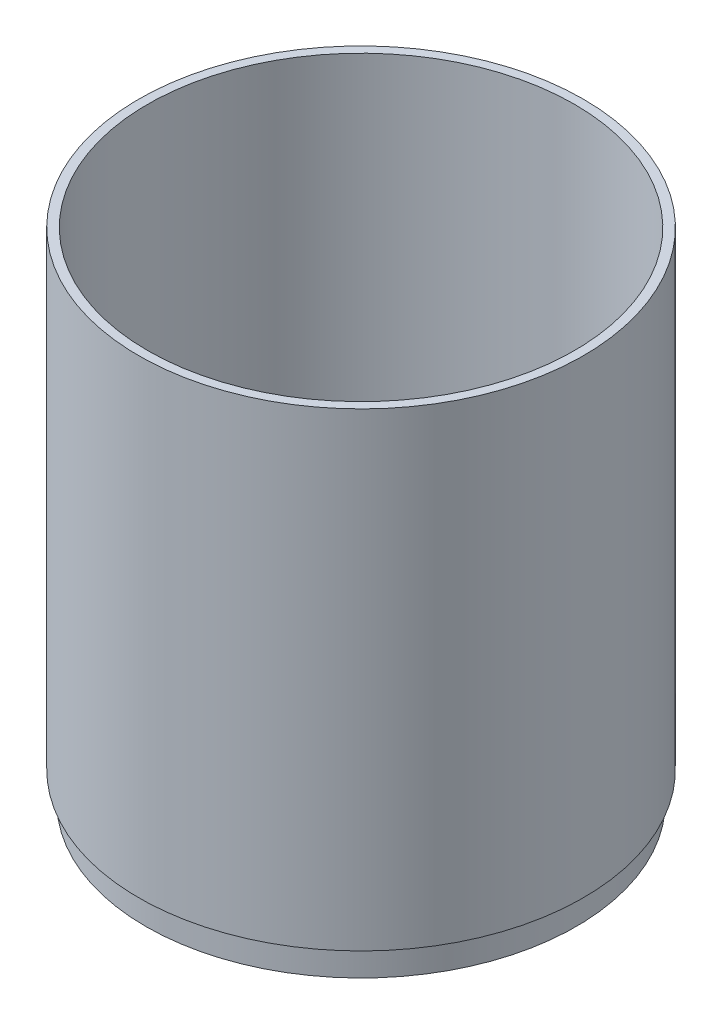
SolidWorks part; units mm, degrees
ref_plane "Front Plane" through (0, 0, 0) normal (0, 0, 1) x (1, 0, 0)
ref_plane "Top Plane" through (0, 0, 0) normal (0, 1, 0) x (1, 0, 0)
ref_plane "Right Plane" through (0, 0, 0) normal (1, 0, 0) x (0, 0, -1)
sketch "Sketch1" plane through (0, 0, 0) normal (0, 0, 1) x (1, 0, 0)
  line L0 (0, 0) -> (0, 40.3893) construction
  line L1 (60.5, 0) -> (15, 0)
  line L2 (60.5, 0) -> (60.5, 8)
  line L3 (60.5, 8) -> (62.5, 8)
  line L4 (62.5, 8) -> (62.5, 140)
  line L5 (62.5, 140) -> (60, 140)
  line L6 (58.5, 10) -> (58.5, 4)
  line L7 (58.5, 4) -> (15, 4)
  line L8 (15, 4) -> (15, 0)
  line L9 (58.5, 10) -> (60, 10)
  line L10 (60, 10) -> (60, 140)
  dimension "D1" = 15
  dimension "D2" = 2
  dimension "D3" = 4
  dimension "D4" = 2
  dimension "D5" = 2
  dimension "D6" = 2.5
  dimension "D7" = 62.5
  dimension "D8" = 140
  dimension "D9" = 8
revolve "Revolve1" add sketch "Sketch1" angle 360 about L0
sketch "Sketch2" plane through (0, 4, 0) normal (0, 1, 0) x (1, 0, 0)
  line L0 (0, 0) -> (0, 58.5) construction
  line L1 (0, 0) -> (-22.387, 54.047)
  line L2 (0, 0) -> (22.387, 54.047)
  line L3 (0, 4) -> (-58.5, 4)
  line L4 (-4, 0) -> (4, 0)
  line L5 (-4, 0) -> (-4, -58.5)
  line L6 (-4, -58.5) -> (4, -58.5)
  line L7 (4, 0) -> (4, -58.5)
  line L8 (0, 4) -> (0, -4)
  line L9 (0, -4) -> (-58.5, -4)
  line L10 (-58.5, 4) -> (-58.5, -4)
  line L11 (4, 0) -> (4, 58.5)
  line L12 (4, 0) -> (-4, 0)
  line L13 (-4, 0) -> (-4, 58.5)
  line L14 (4, 58.5) -> (-4, 58.5)
  line L15 (0, -4) -> (58.5, -4)
  line L16 (0, -4) -> (0, 4)
  line L17 (0, 4) -> (58.5, 4)
  line L18 (58.5, -4) -> (58.5, 4)
  line L19 (0, 0) -> (-4, 0) construction
  line L20 (0, 0) -> (0, 4) construction
  circle A0 centre (0, 0) radius 20
  circle A1 centre (0, 0) radius 58.5
  circle A2 centre (0, 0) radius 58.5
  circle M8 centre (0, 0) radius 58.5
  dimension "D2" = 40
  dimension "D3" = 45
  dimension "D4" = 8
  dimension "D6" = 90
  dimension "D1" = 0
  dimension "D5" = 4
extrude "Cut-Extrude1" cut sketch "Sketch2" against normal blind 10 contours A0 L7 L15 M8 | A0 L17 L2 M8 | A0 L1 L3 M8 | A0 L9 L5 M8
equation "\"R\"=360"
